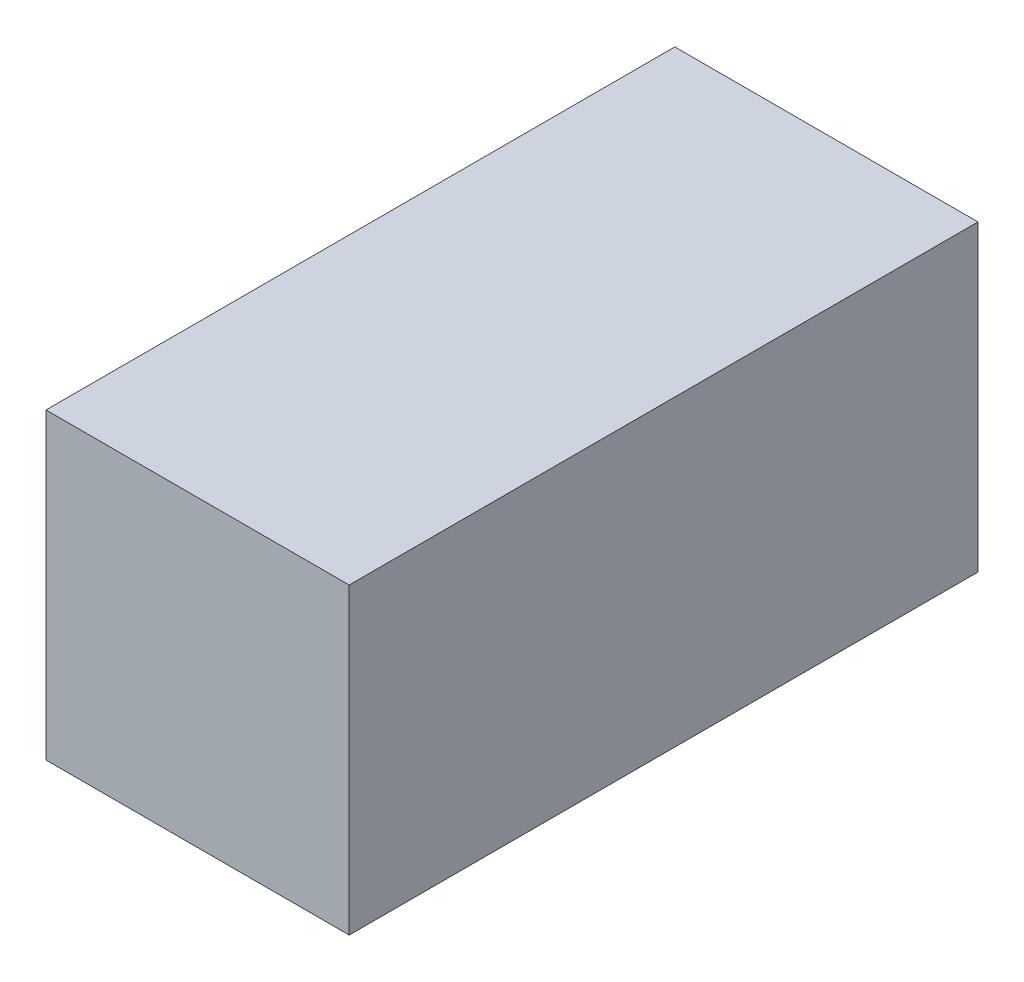
SolidWorks part; units mm, degrees
ref_plane "Front Plane" through (0, 0, 0) normal (0, 0, 1) x (1, 0, 0)
ref_plane "Top Plane" through (0, 0, 0) normal (0, 1, 0) x (1, 0, 0)
ref_plane "Right Plane" through (0, 0, 0) normal (1, 0, 0) x (0, 0, -1)
sketch "Sketch1" plane through (0, 0, 0) normal (0, 1, 0) x (1, 0, 0)
  line L1 (-50, 103.7035) -> (50, 103.7035)
  line L2 (-50, 103.7035) -> (-50, -103.7035)
  line L3 (-50, -103.7035) -> (50, -103.7035)
  line L4 (50, 103.7035) -> (50, -103.7035)
  line L5 (-50, 103.7035) -> (50, -103.7035) construction
  line L6 (-50, -103.7035) -> (50, 103.7035) construction
  point P0 (0, 0)
  dimension "D1" = 207.407
  dimension "D2" = 100
extrude "Boss-Extrude1" add sketch "Sketch1" along normal blind 100
